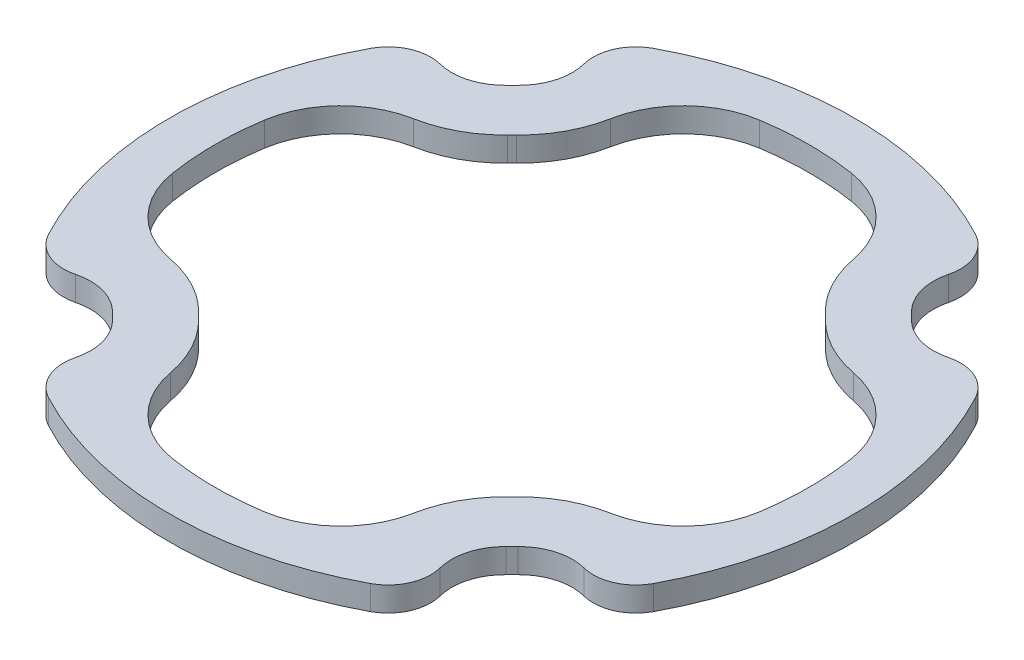
SolidWorks part; units mm, degrees
material "A-Glass Fiber"
ref_plane "Front Plane" through (0, 0, 0) normal (0, 0, 1) x (1, 0, 0)
ref_plane "Top Plane" through (0, 0, 0) normal (0, 1, 0) x (1, 0, 0)
ref_plane "Right Plane" through (0, 0, 0) normal (1, 0, 0) x (0, 0, -1)
sketch "Flange Ref" plane through (0, 0, 0) normal (0, 1, 0) x (1, 0, 0)
  arc A0 (0, 23) -> (-10.8015, 20.3058) centre (0, 0) ccw construction
  arc A1 (-10.8015, 20.3058) -> (-12.4493, 16.5701) centre (-9.2508, 17.3906) ccw construction
  arc A2 (-13.266, 13.6717) -> (-12.4493, 16.5701) centre (-15.3552, 15.8247) ccw construction
  arc A3 (-13.266, 13.6717) -> (-13.6717, 13.266) centre (0, 0) ccw construction
  arc A4 (-16.5701, 12.4493) -> (-13.6717, 13.266) centre (-15.8247, 15.3552) ccw construction
  arc A5 (-16.5701, 12.4493) -> (-17.3906, 12.5528) centre (-17.3906, 9.2508) ccw construction
  arc A6 (-17.3906, 12.5528) -> (-20.3058, 10.8015) centre (-17.3906, 9.2508) ccw construction
  arc A7 (-20.3058, 10.8015) -> (-20.3058, -10.8015) centre (0, 0) ccw construction
  circle A8 centre (0, 0) radius 25 construction
  arc A9 (10.8015, 20.3058) -> (-10.8015, 20.3058) centre (0, 0) ccw construction
  arc A10 (12.5528, 17.3906) -> (10.8015, 20.3058) centre (9.2508, 17.3906) ccw construction
  arc A11 (12.4493, 16.5701) -> (12.5528, 17.3906) centre (9.2508, 17.3906) ccw construction
  arc A12 (12.4493, 16.5701) -> (13.266, 13.6717) centre (15.3552, 15.8247) ccw construction
  arc A13 (13.6717, 13.266) -> (13.266, 13.6717) centre (0, 0) ccw construction
  arc A14 (13.6717, 13.266) -> (16.5701, 12.4493) centre (15.8247, 15.3552) ccw construction
  arc A15 (20.3058, 10.8015) -> (16.5701, 12.4493) centre (17.3906, 9.2508) ccw construction
  arc A16 (23, 0) -> (20.3058, 10.8015) centre (0, 0) ccw construction
  arc A17 (20.3058, -10.8015) -> (20.3058, 10.8015) centre (0, 0) ccw construction
  arc A18 (17.3906, -12.5528) -> (20.3058, -10.8015) centre (17.3906, -9.2508) ccw construction
  arc A19 (16.5701, -12.4493) -> (17.3906, -12.5528) centre (17.3906, -9.2508) ccw construction
  arc A20 (16.5701, -12.4493) -> (13.6717, -13.266) centre (15.8247, -15.3552) ccw construction
  arc A21 (13.266, -13.6717) -> (13.6717, -13.266) centre (0, 0) ccw construction
  arc A22 (13.266, -13.6717) -> (12.4493, -16.5701) centre (15.3552, -15.8247) ccw construction
  arc A23 (10.8015, -20.3058) -> (12.4493, -16.5701) centre (9.2508, -17.3906) ccw construction
  arc A24 (0, -23) -> (10.8015, -20.3058) centre (0, 0) ccw construction
  arc A25 (-10.8015, -20.3058) -> (10.8015, -20.3058) centre (0, 0) ccw construction
  arc A26 (-12.5528, -17.3906) -> (-10.8015, -20.3058) centre (-9.2508, -17.3906) ccw construction
  arc A27 (-12.4493, -16.5701) -> (-12.5528, -17.3906) centre (-9.2508, -17.3906) ccw construction
  arc A28 (-12.4493, -16.5701) -> (-13.266, -13.6717) centre (-15.3552, -15.8247) ccw construction
  arc A29 (-13.6717, -13.266) -> (-13.266, -13.6717) centre (0, 0) ccw construction
  arc A30 (-13.6717, -13.266) -> (-16.5701, -12.4493) centre (-15.8247, -15.3552) ccw construction
  arc A31 (-20.3058, -10.8015) -> (-16.5701, -12.4493) centre (-17.3906, -9.2508) ccw construction
  arc A32 (-23, 0) -> (-20.3058, -10.8015) centre (0, 0) ccw construction
  arc A33 (-4.75, -14.1421) -> (4.75, -14.1421) centre (0, -14.1421) ccw construction
  arc A34 (4.75, -14.1421) -> (-4.75, -14.1421) centre (0, -14.1421) ccw construction
  arc A35 (9.3921, 0) -> (18.8921, 0) centre (14.1421, 0) ccw construction
  arc A36 (18.8921, 0) -> (9.3921, 0) centre (14.1421, 0) ccw construction
  arc A37 (-4.75, 14.1421) -> (4.75, 14.1421) centre (0, 14.1421) ccw construction
  arc A38 (4.75, 14.1421) -> (-4.75, 14.1421) centre (0, 14.1421) ccw construction
  arc A39 (-18.8921, 0) -> (-9.3921, 0) centre (-14.1421, 0) ccw construction
  arc A40 (-9.3921, 0) -> (-18.8921, 0) centre (-14.1421, 0) ccw construction
  point P63 (0, 0)
  dimension "D1" = 50
sketch "Internal Slab" plane through (0, 0, 0) normal (0, 1, 0) x (1, 0, 0)
  arc A0 (19.8644, 10.5667) -> (16.6944, 11.9649) centre (17.3906, 9.2508) ccw
  arc A1 (13.3128, 12.9178) -> (16.6944, 11.9649) centre (15.8247, 15.3552) ccw
  arc A2 (11.9649, 16.6944) -> (12.9178, 13.3128) centre (15.3552, 15.8247) ccw
  arc A3 (12.0528, 17.3906) -> (10.5667, 19.8644) centre (9.2508, 17.3906) ccw
  arc A4 (11.9649, 16.6944) -> (12.0528, 17.3906) centre (9.2508, 17.3906) ccw
  arc A5 (13.3128, 12.9178) -> (12.9178, 13.3128) centre (0, 0) ccw
  arc A6 (10.5667, -19.8644) -> (11.9649, -16.6944) centre (9.2508, -17.3906) ccw
  arc A7 (12.9178, -13.3128) -> (11.9649, -16.6944) centre (15.3552, -15.8247) ccw
  arc A8 (16.6944, -11.9649) -> (13.3128, -12.9178) centre (15.8247, -15.3552) ccw
  arc A9 (17.3906, -12.0528) -> (19.8644, -10.5667) centre (17.3906, -9.2508) ccw
  arc A10 (16.6944, -11.9649) -> (17.3906, -12.0528) centre (17.3906, -9.2508) ccw
  arc A11 (12.9178, -13.3128) -> (13.3128, -12.9178) centre (0, 0) ccw
  arc A12 (-19.8644, -10.5667) -> (-16.6944, -11.9649) centre (-17.3906, -9.2508) ccw
  arc A13 (-13.3128, -12.9178) -> (-16.6944, -11.9649) centre (-15.8247, -15.3552) ccw
  arc A14 (-11.9649, -16.6944) -> (-12.9178, -13.3128) centre (-15.3552, -15.8247) ccw
  arc A15 (-12.0528, -17.3906) -> (-10.5667, -19.8644) centre (-9.2508, -17.3906) ccw
  arc A16 (-11.9649, -16.6944) -> (-12.0528, -17.3906) centre (-9.2508, -17.3906) ccw
  arc A17 (-13.3128, -12.9178) -> (-12.9178, -13.3128) centre (0, 0) ccw
  arc A18 (-19.8644, 10.5667) -> (-19.8644, -10.5667) centre (0, 0) ccw
  arc A19 (10.5667, 19.8644) -> (-10.5667, 19.8644) centre (0, 0) ccw
  arc A20 (19.8644, -10.5667) -> (19.8644, 10.5667) centre (0, 0) ccw
  arc A21 (-10.5667, -19.8644) -> (10.5667, -19.8644) centre (0, 0) ccw
  arc A122 (-10.5667, 19.8644) -> (-11.9649, 16.6944) centre (-9.2508, 17.3906) ccw
  arc A123 (-12.9178, 13.3128) -> (-13.3128, 12.9178) centre (0, 0) ccw
  arc A124 (-12.9178, 13.3128) -> (-11.9649, 16.6944) centre (-15.3552, 15.8247) ccw
  arc A125 (-16.6944, 11.9649) -> (-17.3906, 12.0528) centre (-17.3906, 9.2508) ccw
  arc A126 (-16.6944, 11.9649) -> (-13.3128, 12.9178) centre (-15.8247, 15.3552) ccw
  arc A127 (-17.3906, 12.0528) -> (-19.8644, 10.5667) centre (-17.3906, 9.2508) ccw
  arc A128 (-10.5667, 19.8644) -> (-11.9649, 16.6944) centre (-9.2508, 17.3906) ccw
  arc A129 (-12.9178, 13.3128) -> (-13.3128, 12.9178) centre (0, 0) ccw
  arc A130 (-12.9178, 13.3128) -> (-11.9649, 16.6944) centre (-15.3552, 15.8247) ccw
  arc A131 (-16.6944, 11.9649) -> (-17.3906, 12.0528) centre (-17.3906, 9.2508) ccw
  arc A132 (-16.6944, 11.9649) -> (-13.3128, 12.9178) centre (-15.8247, 15.3552) ccw
  arc A133 (-17.3906, 12.0528) -> (-19.8644, 10.5667) centre (-17.3906, 9.2508) ccw
  point P1 (0, 0)
  point P40 (0, 0)
  dimension "D1" = 0.5
  dimension "D2" = 4
extrude "Boss-Extrude1" add sketch "Internal Slab" along normal blind 1.6
sketch "Sketch3" plane through (0, 0, 0) normal (0, 1, 0) x (1, 0, 0)
  line L0 (0, 0) -> (-31.5542, 0) construction
  line L1 (-31.5542, 0) -> (-33.9533, 6.1655) construction
  line L2 (-33.9533, 6.1655) -> (-33.8659, 6.1654) construction
  line L3 (0, 0) -> (0, 27.5562) construction
  arc A63 (-14.4431, 7.9835) -> (-19.2658, 3.0134) centre (-13.3378, 2.0862) ccw
  arc A65 (-7.9835, 14.4431) -> (-3.0134, 19.2658) centre (-2.0862, 13.3378) cw
  arc A66 (-10.1323, 10.4422) -> (-10.4422, 10.1323) centre (0, 0) ccw
  arc A67 (-10.1323, 10.4422) -> (-8.0904, 17.6883) centre (-15.3552, 15.8247) ccw
  arc A68 (-17.6883, 8.0904) -> (-10.4422, 10.1323) centre (-15.8247, 15.3552) ccw
  arc A69 (-10.1323, 10.4422) -> (-10.4422, 10.1323) centre (0, 0) ccw
  arc A70 (-10.1323, 10.4422) -> (-7.9835, 14.4431) centre (-15.3552, 15.8247) ccw
  arc A71 (-14.4431, 7.9835) -> (-10.4422, 10.1323) centre (-15.8247, 15.3552) ccw
  arc A72 (9.1578, 17.2158) -> (-9.1578, 17.2158) centre (0, 0) ccw
  arc A73 (0, 19.5) -> (-3.0134, 19.2658) centre (0, 0) ccw
  arc A74 (3.0134, 19.2658) -> (0, 19.5) centre (0, 0) ccw
  arc A75 (7.9835, 14.4431) -> (3.0134, 19.2658) centre (2.0862, 13.3378) ccw
  arc A76 (7.9835, 14.4431) -> (10.1323, 10.4422) centre (15.3552, 15.8247) ccw
  arc A77 (10.4422, 10.1323) -> (10.1323, 10.4422) centre (0, 0) ccw
  arc A78 (10.4422, 10.1323) -> (14.4431, 7.9835) centre (15.8247, 15.3552) ccw
  arc A79 (14.4431, 7.9835) -> (19.2658, 3.0134) centre (13.3378, 2.0862) cw
  arc A80 (19.5, 0) -> (19.2658, 3.0134) centre (0, 0) ccw
  arc A81 (19.2658, -3.0134) -> (19.5, 0) centre (0, 0) ccw
  arc A82 (14.4431, -7.9835) -> (19.2658, -3.0134) centre (13.3378, -2.0862) ccw
  arc A83 (14.4431, -7.9835) -> (10.4422, -10.1323) centre (15.8247, -15.3552) ccw
  arc A84 (10.1323, -10.4422) -> (10.4422, -10.1323) centre (0, 0) ccw
  arc A85 (10.1323, -10.4422) -> (7.9835, -14.4431) centre (15.3552, -15.8247) ccw
  arc A86 (7.9835, -14.4431) -> (3.0134, -19.2658) centre (2.0862, -13.3378) cw
  arc A87 (0, -19.5) -> (3.0134, -19.2658) centre (0, 0) ccw
  arc A88 (-3.0134, -19.2658) -> (0, -19.5) centre (0, 0) ccw
  arc A89 (-7.9835, -14.4431) -> (-3.0134, -19.2658) centre (-2.0862, -13.3378) ccw
  arc A90 (-7.9835, -14.4431) -> (-10.1323, -10.4422) centre (-15.3552, -15.8247) ccw
  arc A91 (-10.4422, -10.1323) -> (-10.1323, -10.4422) centre (0, 0) ccw
  arc A92 (-10.4422, -10.1323) -> (-14.4431, -7.9835) centre (-15.8247, -15.3552) ccw
  arc A93 (-14.4431, -7.9835) -> (-19.2658, -3.0134) centre (-13.3378, -2.0862) cw
  arc A94 (-19.5, 0) -> (-19.2658, -3.0134) centre (0, 0) ccw
  arc A146 (-17.2158, 9.1578) -> (-17.2158, -9.1578) centre (0, 0) ccw
  arc A147 (-19.2658, 3.0134) -> (-19.5, 0) centre (0, 0) ccw
  point P57 (0, 0)
  dimension "D3" = 6
  dimension "D5" = 6
  dimension "D1" = 3
  dimension "D2" = 4
  dimension "D4" = 3
  dimension "D6" = 4
extrude "Cut-Extrude2" cut sketch "Sketch3" along normal through all
sketch "Sketch4" [suppressed] plane through (0, 1.6, 0) normal (0, 1, 0) x (1, 0, 0)
  line L0 (0, 0) -> (0, 23.3583)
  line L1 (0, 0) -> (6.0456, 22.5624)
  line L2 (0, 0) -> (11.6791, 20.2289)
  line L3 (0, 0) -> (16.5168, 16.5168)
  line L4 (0, 0) -> (20.2289, 11.6791)
  line L5 (0, 0) -> (22.5624, 6.0456)
  line L6 (0, 0) -> (23.3583, 0)
  line L7 (0, 0) -> (22.5624, -6.0456)
  line L8 (0, 0) -> (20.2289, -11.6791)
  line L9 (0, 0) -> (16.5168, -16.5168)
  line L10 (0, 0) -> (11.6791, -20.2289)
  line L11 (0, 0) -> (6.0456, -22.5624)
  line L12 (0, 0) -> (0, -23.3583)
  line L13 (0, 0) -> (-6.0456, -22.5624)
  line L14 (0, 0) -> (-11.6791, -20.2289)
  line L15 (0, 0) -> (-16.5168, -16.5168)
  line L16 (0, 0) -> (-20.2289, -11.6791)
  line L17 (0, 0) -> (-22.5624, -6.0456)
  line L18 (0, 0) -> (-23.3583, 0)
  line L19 (0, 0) -> (-22.5624, 6.0456)
  line L20 (0, 0) -> (-20.2289, 11.6791)
  line L21 (0, 0) -> (-16.5168, 16.5168)
  line L22 (0, 0) -> (-11.6791, 20.2289)
  line L23 (0, 0) -> (-6.0456, 22.5624)
  arc A93 (18.5401, -9.8623) -> (18.5401, 9.8623) centre (0, 0) ccw
  arc A94 (18.5401, 9.8623) -> (17.0671, 10.512) centre (17.3906, 9.2508) ccw
  arc A95 (12.2363, 11.8733) -> (17.0671, 10.512) centre (15.8247, 15.3552) ccw
  arc A96 (12.2363, 11.8733) -> (11.8733, 12.2363) centre (0, 0) ccw
  arc A97 (10.512, 17.0671) -> (11.8733, 12.2363) centre (15.3552, 15.8247) ccw
  arc A98 (10.512, 17.0671) -> (9.8623, 18.5401) centre (9.2508, 17.3906) ccw
  arc A99 (9.8623, 18.5401) -> (-9.8623, 18.5401) centre (0, 0) ccw
  arc A100 (-9.8623, 18.5401) -> (-10.512, 17.0671) centre (-9.2508, 17.3906) ccw
  arc A101 (-11.8733, 12.2363) -> (-10.512, 17.0671) centre (-15.3552, 15.8247) ccw
  arc A102 (-11.8733, 12.2363) -> (-12.2363, 11.8733) centre (0, 0) ccw
  arc A103 (-17.0671, 10.512) -> (-12.2363, 11.8733) centre (-15.8247, 15.3552) ccw
  arc A104 (-17.0671, 10.512) -> (-18.5401, 9.8623) centre (-17.3906, 9.2508) ccw
  arc A105 (-18.5401, 9.8623) -> (-18.5401, -9.8623) centre (0, 0) ccw
  arc A106 (-18.5401, -9.8623) -> (-17.0671, -10.512) centre (-17.3906, -9.2508) ccw
  arc A107 (-12.2363, -11.8733) -> (-17.0671, -10.512) centre (-15.8247, -15.3552) ccw
  arc A108 (-12.2363, -11.8733) -> (-11.8733, -12.2363) centre (0, 0) ccw
  arc A109 (-10.512, -17.0671) -> (-11.8733, -12.2363) centre (-15.3552, -15.8247) ccw
  arc A110 (-10.512, -17.0671) -> (-9.8623, -18.5401) centre (-9.2508, -17.3906) ccw
  arc A111 (-9.8623, -18.5401) -> (9.8623, -18.5401) centre (0, 0) ccw
  arc A112 (9.8623, -18.5401) -> (10.512, -17.0671) centre (9.2508, -17.3906) ccw
  arc A113 (11.8733, -12.2363) -> (10.512, -17.0671) centre (15.3552, -15.8247) ccw
  arc A114 (11.8733, -12.2363) -> (12.2363, -11.8733) centre (0, 0) ccw
  arc A115 (17.0671, -10.512) -> (12.2363, -11.8733) centre (15.8247, -15.3552) ccw
  arc A116 (17.0671, -10.512) -> (18.5401, -9.8623) centre (17.3906, -9.2508) ccw
  arc A117 (18.5401, -9.8623) -> (18.5401, 9.8623) centre (0, 0) ccw
  arc A118 (18.5401, 9.8623) -> (17.0671, 10.512) centre (17.3906, 9.2508) ccw
  arc A119 (12.2363, 11.8733) -> (17.0671, 10.512) centre (15.8247, 15.3552) ccw
  arc A120 (12.2363, 11.8733) -> (11.8733, 12.2363) centre (0, 0) ccw
  arc A121 (10.512, 17.0671) -> (11.8733, 12.2363) centre (15.3552, 15.8247) ccw
  arc A122 (10.512, 17.0671) -> (9.8623, 18.5401) centre (9.2508, 17.3906) ccw
  arc A123 (9.8623, 18.5401) -> (-9.8623, 18.5401) centre (0, 0) ccw
  arc A124 (-9.8623, 18.5401) -> (-10.512, 17.0671) centre (-9.2508, 17.3906) ccw
  arc A125 (-11.8733, 12.2363) -> (-10.512, 17.0671) centre (-15.3552, 15.8247) ccw
  arc A126 (-11.8733, 12.2363) -> (-12.2363, 11.8733) centre (0, 0) ccw
  arc A127 (-17.0671, 10.512) -> (-12.2363, 11.8733) centre (-15.8247, 15.3552) ccw
  arc A128 (-17.0671, 10.512) -> (-18.5401, 9.8623) centre (-17.3906, 9.2508) ccw
  arc A129 (-18.5401, 9.8623) -> (-18.5401, -9.8623) centre (0, 0) ccw
  arc A130 (-18.5401, -9.8623) -> (-17.0671, -10.512) centre (-17.3906, -9.2508) ccw
  arc A131 (-12.2363, -11.8733) -> (-17.0671, -10.512) centre (-15.8247, -15.3552) ccw
  arc A132 (-12.2363, -11.8733) -> (-11.8733, -12.2363) centre (0, 0) ccw
  arc A133 (-10.512, -17.0671) -> (-11.8733, -12.2363) centre (-15.3552, -15.8247) ccw
  arc A134 (-10.512, -17.0671) -> (-9.8623, -18.5401) centre (-9.2508, -17.3906) ccw
  arc A135 (-9.8623, -18.5401) -> (9.8623, -18.5401) centre (0, 0) ccw
  arc A136 (9.8623, -18.5401) -> (10.512, -17.0671) centre (9.2508, -17.3906) ccw
  arc A137 (11.8733, -12.2363) -> (10.512, -17.0671) centre (15.3552, -15.8247) ccw
  arc A138 (11.8733, -12.2363) -> (12.2363, -11.8733) centre (0, 0) ccw
  arc A139 (17.0671, -10.512) -> (12.2363, -11.8733) centre (15.8247, -15.3552) ccw
  arc A140 (17.0671, -10.512) -> (18.5401, -9.8623) centre (17.3906, -9.2508) ccw
  point P0 (0, 0)
  point P29 (0, 0)
  dimension "D2" = 1.5
  dimension "D1" = 24
